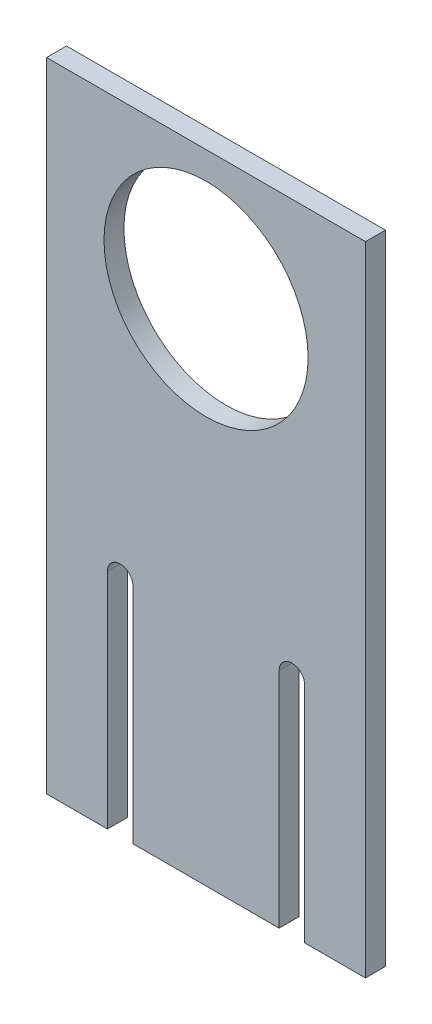
SolidWorks part; units mm, degrees
ref_plane "Plano frontal" through (0, 0, 0) normal (0, 0, 1) x (1, 0, 0)
ref_plane "Plano superior" through (0, 0, 0) normal (0, 1, 0) x (1, 0, 0)
ref_plane "Plano direito" through (0, 0, 0) normal (1, 0, 0) x (0, 0, -1)
sketch "Esboço1" plane through (0, 0, 0) normal (0, 0, 1) x (1, 0, 0)
  line L1 (0, 0) -> (-50, 0)
  line L2 (0, 0) -> (0, 100)
  line L3 (0, 100) -> (-50, 100)
  line L4 (-50, 0) -> (-50, 100)
extrude "Ressalto-extrusão1" add sketch "Esboço1" along normal blind 3.125
sketch "Esboço2" plane through (0, 0, 3.125) normal (0, 0, 1) x (1, 0, 0)
  line L0 (-25, 100) -> (-25, 0) construction
  line L1 (0, 100) -> (-50, 100) construction
  line L2 (-50, 0) -> (0, 0) construction
  line L3 (-36.4647, 35) -> (-36.4647, 0)
  line L4 (-36.4647, 0) -> (-40.4647, 0)
  line L5 (-40.4647, 0) -> (-40.4647, 35)
  line L6 (-13.5353, 35) -> (-13.5353, 0)
  line L7 (-9.5353, 0) -> (-9.5353, 35)
  line L8 (-13.5353, 0) -> (-9.5353, 0)
  circle A0 centre (-25, 79.7128) radius 16
  arc A1 (-36.4647, 35) -> (-40.4647, 35) centre (-38.4647, 35) ccw
  arc A2 (-13.5353, 35) -> (-9.5353, 35) centre (-11.5353, 35) cw
extrude "Corte-extrusão1" cut sketch "Esboço2" against normal blind 3.125
